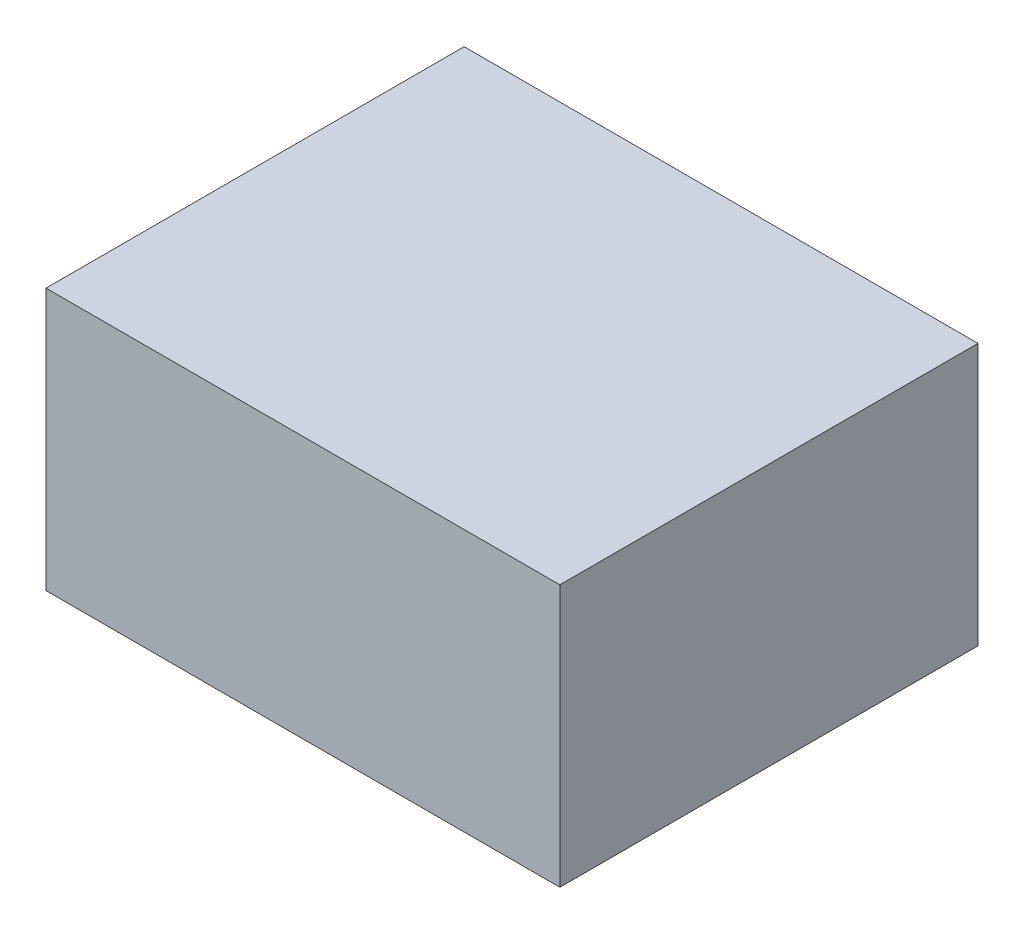
SolidWorks part; units mm, degrees
ref_plane "Front Plane" through (0, 0, 0) normal (0, 0, 1) x (1, 0, 0)
ref_plane "Top Plane" through (0, 0, 0) normal (0, 1, 0) x (1, 0, 0)
ref_plane "Right Plane" through (0, 0, 0) normal (1, 0, 0) x (0, 0, -1)
sketch "Sketch1" plane through (0, 0, 0) normal (0, 0, 1) x (1, 0, 0)
  line L1 (-25.5, -13) -> (25.5, -13)
  line L2 (-25.5, -13) -> (-25.5, 13)
  line L3 (-25.5, 13) -> (25.5, 13)
  line L4 (25.5, -13) -> (25.5, 13)
  line L5 (-25.5, -13) -> (25.5, 13) construction
  line L6 (-25.5, 13) -> (25.5, -13) construction
  point P0 (0, 0)
  dimension "D1" = 51
  dimension "D2" = 26
extrude "Boss-Extrude1" add sketch "Sketch1" along normal blind 41.5
